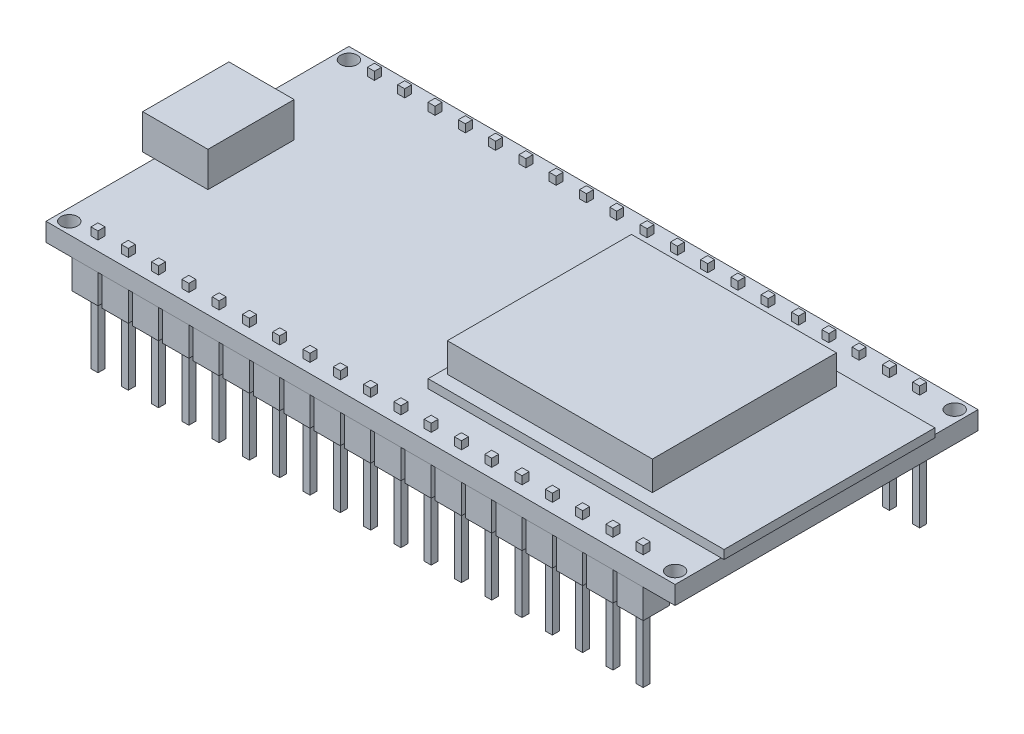
SolidWorks part; units mm, degrees
ref_plane "Front Plane" through (0, 0, 0) normal (0, 0, 1) x (1, 0, 0)
ref_plane "Top Plane" through (0, 0, 0) normal (0, 1, 0) x (1, 0, 0)
ref_plane "Right Plane" through (0, 0, 0) normal (1, 0, 0) x (0, 0, -1)
sketch "Sketch1" plane through (0, 0, 0) normal (0, 1, 0) x (1, 0, 0)
  line L1 (-27, -13) -> (27, -13)
  line L2 (-27, -13) -> (-27, 13)
  line L3 (-27, 13) -> (27, 13)
  line L4 (27, -13) -> (27, 13)
  line L5 (-27, -13) -> (27, 13) construction
  line L6 (-27, 13) -> (27, -13) construction
  point P0 (0, 0)
  dimension "D1" = 54
  dimension "D2" = 26
extrude "Boss-Extrude1" add sketch "Sketch1" along normal mid plane 1.57
sketch "Sketch2" plane through (0, 0.785, 0) normal (0, 1, 0) x (1, 0, 0)
  line L0 (-27, 13) -> (-27, -13) construction
  line L1 (27, 13) -> (-27, 13) construction
  circle A0 centre (-26, 12) radius 0.71
  dimension "D1" = 1.42
  dimension "D2" = 1
  dimension "D3" = 1
sketch3d "3DSketch1"
  line L0 (-36.4495, 0, 0) -> (36.4495, 0, 0) construction
  line L1 (0, -12.7979, 0) -> (0, 12.7979, 0) construction
  point P2 (0, 0, 0)
  point P6 (0, 0, 0)
extrude "Cut-Extrude1" cut sketch "Sketch2" against normal through all
mirror "Mirror1" about plane through (0, 0, 0) normal (1, 0, 0) of "Cut-Extrude1"
mirror "Mirror2" about plane through (0, 0, 0) normal (0, 0, 1) of "Mirror1", "Cut-Extrude1"
sketch "Sketch3" plane through (0, 0.785, 0) normal (0, 1, 0) x (1, 0, 0)
  line L0 (-36.4495, 0) -> (36.4495, 0) construction
  line L1 (-28, 3.7) -> (-22.4, 3.7)
  line L2 (-28, 3.7) -> (-28, -3.7)
  line L3 (-28, -3.7) -> (-22.4, -3.7)
  line L4 (-22.4, 3.7) -> (-22.4, -3.7)
  line L5 (-28, 3.7) -> (-22.4, -3.7) construction
  line L6 (-28, -3.7) -> (-22.4, 3.7) construction
  line L7 (-27, 13) -> (-27, -13) construction
  point P0 (-25.2, 0)
  dimension "D1" = 5.6
  dimension "D2" = 7.4
  dimension "D3" = 1
extrude "Boss-Extrude2" add sketch "Sketch3" along normal blind 3
sketch "Sketch4" plane through (0, 0.785, 0) normal (0, 1, 0) x (1, 0, 0)
  line L0 (-36.4495, 0) -> (36.4495, 0) construction
  line L1 (1.85, -9.05) -> (27.25, -9.05)
  line L2 (1.85, -9.05) -> (1.85, 9.05)
  line L3 (1.85, 9.05) -> (27.25, 9.05)
  line L4 (27.25, -9.05) -> (27.25, 9.05)
  line L5 (1.85, -9.05) -> (27.25, 9.05) construction
  line L6 (1.85, 9.05) -> (27.25, -9.05) construction
  line L7 (27, -13) -> (27, 13) construction
  point P0 (14.55, 0)
  dimension "D1" = 18.1
  dimension "D2" = 25.4
  dimension "D3" = 0.25
extrude "Boss-Extrude3" add sketch "Sketch4" along normal blind 0.75
sketch "Sketch5" plane through (0, 1.535, 0) normal (0, 1, 0) x (1, 0, 0)
  line L0 (-36.4495, 0) -> (36.4495, 0) construction
  line L1 (2.35, -7.9) -> (19.95, -7.9)
  line L2 (2.35, -7.9) -> (2.35, 7.9)
  line L3 (2.35, 7.9) -> (19.95, 7.9)
  line L4 (19.95, -7.9) -> (19.95, 7.9)
  line L5 (2.35, -7.9) -> (19.95, 7.9) construction
  line L6 (2.35, 7.9) -> (19.95, -7.9) construction
  line L7 (1.85, 9.05) -> (1.85, -9.05) construction
  point P0 (11.15, 0)
  dimension "D1" = 17.6
  dimension "D2" = 15.8
  dimension "D3" = 0.5
extrude "Boss-Extrude4" add sketch "Sketch5" along normal blind 2.5
sketch "Sketch6" plane through (0, -0.785, 0) normal (0, -1, 0) x (1, 0, 0)
  line L1 (-24.7988, -12.99) -> (-22.5488, -12.99)
  line L2 (-24.7988, -12.99) -> (-24.7988, -10.74)
  line L3 (-24.7988, -10.74) -> (-22.5488, -10.74)
  line L4 (-22.5488, -12.99) -> (-22.5488, -10.74)
  line L5 (-24.7988, -12.99) -> (-22.5488, -10.74) construction
  line L6 (-24.7988, -10.74) -> (-22.5488, -12.99) construction
  line L7 (27, -13) -> (-27, -13) construction
  circle A0 centre (-26, -12) radius 0.71 construction
  point P0 (-23.6738, -11.865)
  point P9 (-25.2988, -11.8886)
  dimension "D1" = 2.25
  dimension "D2" = 2.25
  dimension "D3" = 0.5
  dimension "D4" = 0.01
extrude "Boss-Extrude5" add sketch "Sketch6" along normal blind 2.5
sketch "Sketch7" plane through (0, -3.285, 0) normal (0, -1, 0) x (1, 0, 0)
  line L0 (-22.5488, -10.74) -> (-24.7988, -10.74) construction
  line L1 (-23.9738, -12.165) -> (-23.3738, -12.165)
  line L2 (-23.9738, -12.165) -> (-23.9738, -11.565)
  line L3 (-23.9738, -11.565) -> (-23.3738, -11.565)
  line L4 (-23.3738, -12.165) -> (-23.3738, -11.565)
  line L5 (-23.9738, -12.165) -> (-23.3738, -11.565) construction
  line L6 (-23.9738, -11.565) -> (-23.3738, -12.165) construction
  line L7 (-24.7988, -10.74) -> (-24.7988, -12.99) construction
  point P0 (-23.6738, -11.865)
  point P8 (-23.6738, -10.74)
  point P12 (-24.7988, -11.865)
  dimension "D1" = 0.6
extrude "Boss-Extrude6" add sketch "Sketch7" along normal blind 5.8 and the other way blind 4.75
pattern_linear "LPattern1" count 19 spacing 2.6 along (1, 0, 0) of "Boss-Extrude5", "Boss-Extrude6"
mirror "Mirror3" about plane through (0, 0, 0) normal (0, 0, 1) of "LPattern1", "Boss-Extrude5", "Boss-Extrude6"
